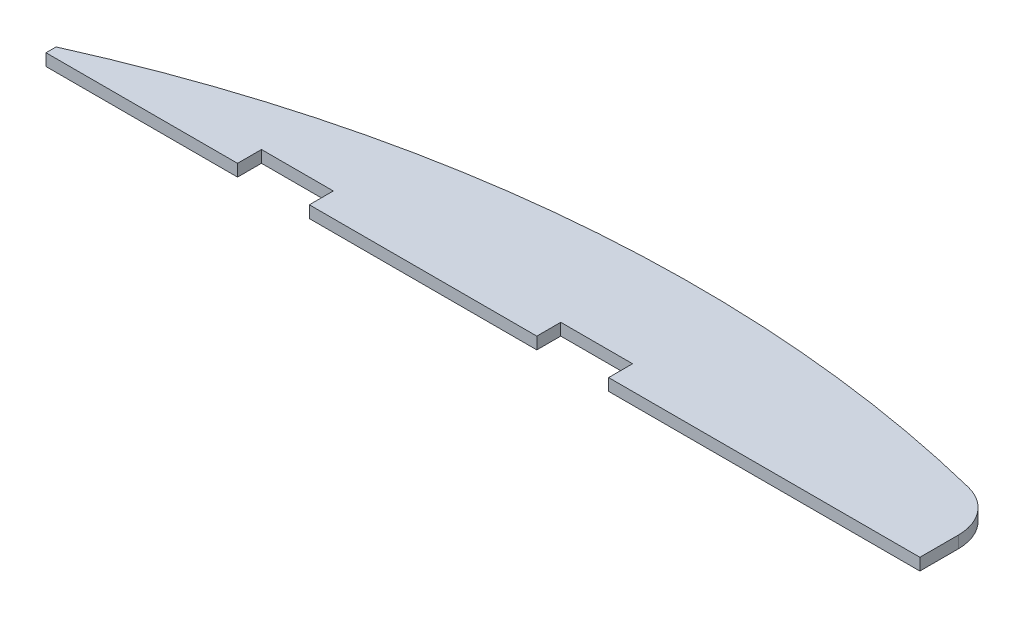
SolidWorks part; units mm, degrees
ref_plane "前视基准面" through (0, 0, 0) normal (0, 0, 1) x (1, 0, 0)
ref_plane "上视基准面" through (0, 0, 0) normal (0, 1, 0) x (1, 0, 0)
ref_plane "右视基准面" through (0, 0, 0) normal (1, 0, 0) x (0, 0, -1)
other "Configuration Table"
sketch "草图1" plane through (0, 0, 0) normal (0, 1, 0) x (1, 0, 0)
  line L0 (-30, -3) -> (-44, -3)
  line L1 (-30, 3) -> (30, 3) construction
  line L2 (-30, 3) -> (-30, -3) construction
  line L3 (-30, -3) -> (30, -3) construction
  line L4 (30, 3) -> (30, -3) construction
  line L5 (-30, 3) -> (30, -3) construction
  line L6 (-30, -3) -> (30, 3) construction
  line L7 (30, -3) -> (29, -3) construction
  line L9 (-44, 25.6817) -> (44, 25.6817) construction
  line L10 (-44, -2.1583) -> (-44, -3)
  line L11 (-44, -25.6817) -> (44, -25.6817) construction
  line L12 (29, 3.286) -> (29, -3)
  line L13 (-44, 25.6817) -> (44, -25.6817) construction
  line L14 (-44, -25.6817) -> (44, 25.6817) construction
  line L16 (0, -3) -> (29, -3)
  line L17 (-30, -3) -> (0, -3)
  arc A0 (29, 3.286) -> (-44, -2.1583) centre (0, -100) ccw
  point P0 (0, 0)
  point P7 (0, 0)
  dimension "D1" = 6
  dimension "D2" = 100
  dimension "D3" = 60
  dimension "D4" = 44
  dimension "D5" = 29
extrude "凸台-拉伸1" add sketch "草图1" along normal blind 1
sketch "草图2" plane through (0, 0, 0) normal (0, -1, 0) x (1, 0, 0)
  line L5 (-44, 3) -> (29, 3) construction
  line L6 (-3, 5) -> (3, 5)
  line L16 (-3, 5) -> (-3, 1)
  line L17 (0, 0) -> (0, 11.1642) construction
  line L18 (-3, 1) -> (3, 1)
  line L19 (3, 5) -> (3, 1)
  line L20 (-3, 5) -> (3, 1) construction
  line L21 (-3, 1) -> (3, 5) construction
  line L22 (-28, 5) -> (-22, 5)
  line L23 (-28, 5) -> (-28, 1)
  line L24 (-28, 1) -> (-22, 1)
  line L25 (-22, 5) -> (-22, 1)
  line L26 (-25, 0) -> (-25, 11.1642) construction
  line L27 (-28, 5) -> (-22, 1) construction
  line L28 (-28, 1) -> (-22, 5) construction
  line L29 (0, 3) -> (-25, 3) construction
  point P0 (0, 3)
  point P7 (-25, 3)
  dimension "D1" = 4
  dimension "D2" = 6
  dimension "D4" = 25
  dimension "D3" = 2
extrude "切除-拉伸1" cut sketch "草图2" against normal through all
fillet "圆角1" radius 4 1 edges at (29, 0.5, -3.286)
